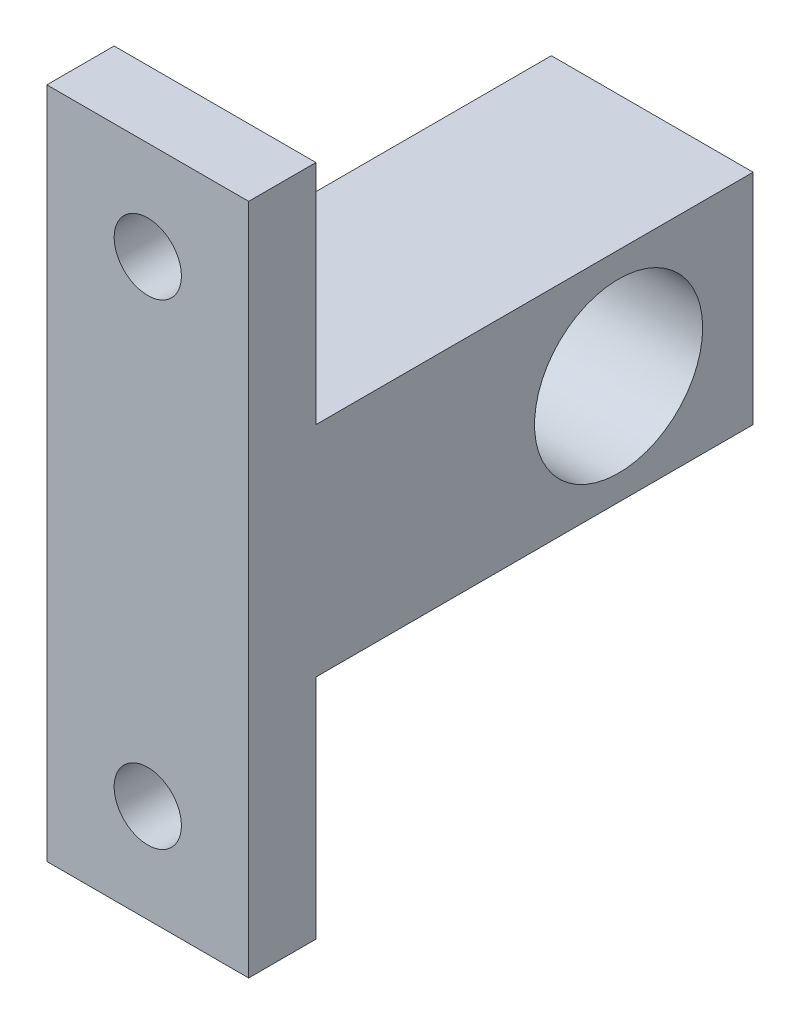
SolidWorks part; units mm, degrees
ref_plane "Front Plane" through (0, 0, 0) normal (0, 0, 1) x (1, 0, 0)
ref_plane "Top Plane" through (0, 0, 0) normal (0, 1, 0) x (1, 0, 0)
ref_plane "Right Plane" through (0, 0, 0) normal (1, 0, 0) x (0, 0, -1)
sketch "Sketch1" plane through (0, 0, 0) normal (1, 0, 0) x (0, 0, -1)
  line L0 (-22, -20) -> (-22, 20)
  line L1 (-22, 20) -> (-18, 20)
  line L2 (-18, 20) -> (-18, 6.5)
  line L3 (-18, 6.5) -> (8, 6.5)
  line L4 (8, 6.5) -> (8, -6.5)
  line L5 (55, 0) -> (-55, 0) construction
  line L6 (-18, -6.5) -> (8, -6.5)
  line L7 (-18, -20) -> (-18, -6.5)
  line L8 (-22, -20) -> (-18, -20)
  circle A0 centre (0, 0) radius 5
  point P12 (8, 0)
  point P15 (-22, 0)
  dimension "D1" = 30
  dimension "D2" = 13
  dimension "D3" = 8
  dimension "D4" = 4
  dimension "D5" = 40
extrude "Boss-Extrude1" add sketch "Sketch1" along normal mid plane 12
sketch "Sketch2" plane through (0, 0, 18) normal (0, 0, -1) x (-1, 0, 0)
  line L0 (6.6, 0) -> (-6.6, 0) construction
  circle A0 centre (0, 14.1497) radius 2
  circle A1 centre (0, -14.1497) radius 2
extrude "Cut-Extrude1" cut sketch "Sketch2" against normal through all
